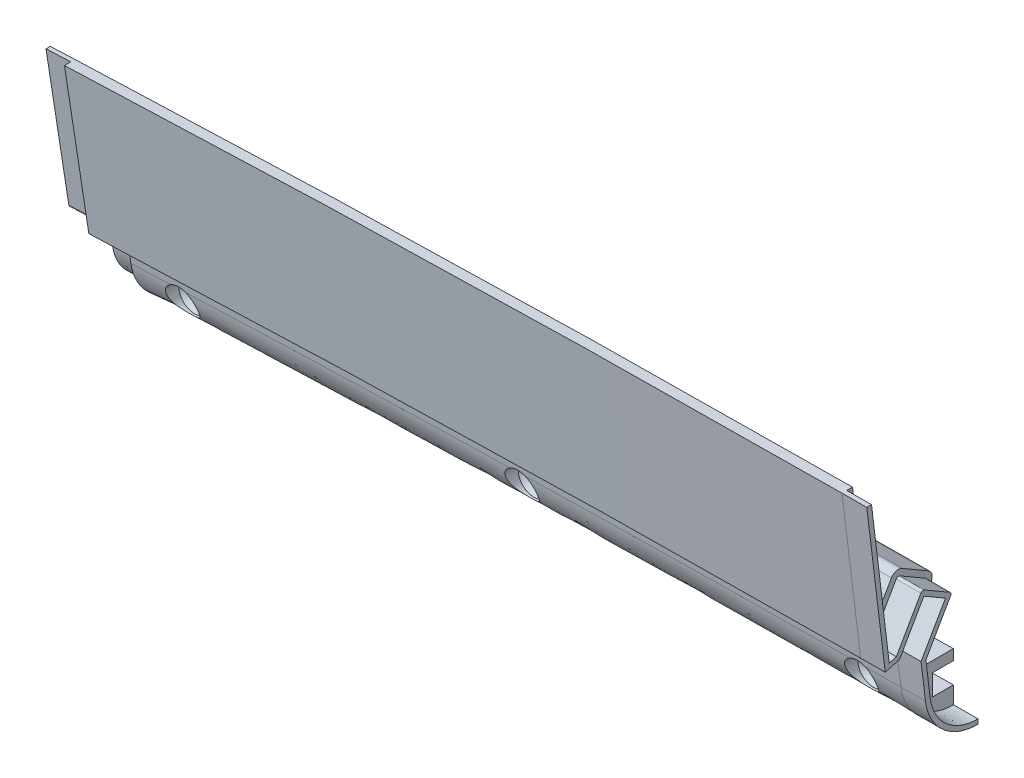
SolidWorks part; units mm, degrees
ref_plane "Front Plane" through (0, 0, 0) normal (0, 0, 1) x (1, 0, 0)
ref_plane "Top Plane" through (0, 0, 0) normal (0, 1, 0) x (1, 0, 0)
ref_plane "Right Plane" through (0, 0, 0) normal (1, 0, 0) x (0, 0, -1)
ref_plane "Plane3" through (-117.056, -3.871, 0) normal (0.9995, 0.0331, 0) x (0, 0, -1)
sketch "Sketch2" plane through (-117.056, -3.871, 0) normal (0.9995, 0.0331, 0) x (0, 0, -1)
  line L0 (-101.6, -41.1511) -> (-101.6, -45.9265)
  line L1 (-101.6, -41.1511) -> (-101.6, -45.9265)
  line L2 (-106.68, -45.9265) -> (-106.68, -50.6257)
  line L3 (-106.68, -45.9265) -> (-106.68, -50.6257)
  line L4 (-101.6, -50.6257) -> (-106.68, -50.6257)
  line L5 (-101.6, -50.6257) -> (-106.68, -50.6257)
  line L6 (-101.6, -50.6257) -> (-101.6, -56.1377)
  line L7 (-101.6, -50.6257) -> (-101.6, -56.1377)
  line L8 (-106.68, -45.9265) -> (-101.6, -45.9265)
  line L9 (-106.68, -45.9265) -> (-101.6, -45.9265)
  line L10 (-106.8705, -50.8162) -> (-108.9961, -53.9781) construction
  line L11 (-101.7905, -43.196) -> (-101.7905, -45.736)
  line L12 (-106.8705, -45.736) -> (-101.7905, -45.736)
  line L13 (-106.8705, -45.736) -> (-106.8705, -50.8162)
  line L14 (-101.7905, -50.8162) -> (-106.8705, -50.8162)
  line L15 (-101.7905, -50.8162) -> (-101.7905, -56.1377)
  line L16 (-101.7905, -43.196) -> (-101.6, -43.196)
  line L17 (-101.7905, -41.1511) -> (-101.7905, -45.736) construction
  line L18 (-120.8053, -33.0481) -> (-115.57, -36.0708)
  line L19 (-120.8053, -33.0481) -> (-115.57, -36.0708)
  line L20 (-109.601, -25.7318) -> (-114.8363, -22.709)
  line L21 (-109.601, -25.7318) -> (-114.8363, -22.709)
  line L22 (-114.8363, -22.709) -> (-120.8053, -33.0481)
  line L23 (-114.8363, -22.709) -> (-120.8053, -33.0481)
  line L24 (-115.57, -36.0708) -> (-109.601, -25.7318)
  line L25 (-115.57, -36.0708) -> (-109.601, -25.7318)
  line L26 (-115.57, -36.0708) -> (-114.523, -44.9291)
  line L28 (-118.1876, -34.5595) -> (-112.2186, -24.2204) construction
  line L29 (-114.6403, -39.5406) -> (-107.0838, -26.4518)
  line L30 (-107.7811, -23.8496) -> (-114.1162, -20.1918)
  line L31 (-116.7185, -20.8891) -> (-124.2749, -33.9778)
  line L33 (-106.1314, -24.8021) -> (-115.766, -19.2393) construction
  line L34 (-115.766, -19.2393) -> (-124.2749, -33.9778) construction
  line L35 (-114.6403, -39.5406) -> (-106.1314, -24.8021) construction
  line L36 (-124.2749, -33.9778) -> (-114.6403, -39.5406) construction
  line L37 (-112.9486, -36.6103) -> (-112.1701, -43.196)
  line L38 (-124.2749, -33.9778) -> (-128.0422, -2.1051)
  line L39 (-128.0422, -2.1051) -> (-132.6063, -0.4439)
  line L40 (-50.8, 0.7495) -> (-2184.4, 0.7495)
  line L41 (-125.822, 0.7495) -> (-133.442, 0.7495)
  line L42 (-122.1519, -30.3004) -> (-125.822, 0.7495)
  arc A0 (-114.523, -44.9291) -> (-101.7905, -56.1377) centre (-101.9108, -43.4383) ccw
  arc A2 (-114.1162, -20.1918) -> (-116.7185, -20.8891) centre (-115.0687, -21.8416) ccw
  arc A3 (-107.0838, -26.4518) -> (-107.7811, -23.8496) centre (-108.7336, -25.4993) ccw
  arc A4 (-133.442, 0.7495) -> (-132.6063, -0.4439) centre (-132.172, 0.7495) ccw
  point P21 (-107.6337, -51.6514)
  point P22 (0, 0)
  point P40 (994.1925, -42.034)
  point P41 (-133.442, 0.7495)
  point P42 (986.21, -13.8823)
  point P45 (980.8261, -8.8265)
  point P46 (985.0704, -9.8607)
  point P49 (-101.6, -43.196)
  dimension "D2" = 25.4
  dimension "D6" = 1.905
  dimension "D8" = 2.54
  dimension "D4" = 2.54
  dimension "D5" = 2.54
  dimension "D7" = 2.54
  dimension "D9" = 2.54
  dimension "D10" = 20
  dimension "D11" = 7.62
  dimension "D12" = 3.81
  dimension "D3" = 0.1905
sketch "Sketch3" plane through (0, 0, 101.6) normal (0, 0, 1) x (1, 0, 0)
  arc A0 (622.1039, -83.1998) -> (-622.1039, -83.1998) centre (0, -4954.4862) ccw construction
  arc A1 (622.1039, -83.1998) -> (-622.1039, -83.1998) centre (0, -4954.4862) ccw
sketch "Sketch4" plane through (-117.3306, 4.4304, 1117.6) normal (0.9995, 0.0331, 0) x (0, 0, -1)
  line L29 (1009.8189, -32.1556) -> (1003.4838, -28.4978) construction
  line L32 (1000.8815, -29.1951) -> (993.3251, -42.2838) construction
  line L35 (993.3251, -42.2838) -> (989.5578, -10.4111) construction
  line L50 (995.4481, -38.6064) -> (991.778, -7.5565) construction
  line L51 (1002.03, -44.3768) -> (1003.077, -53.235) construction
  line L52 (1015.8095, -59.1222) -> (1015.8095, -64.4437) construction
  line L53 (1015.8095, -59.1222) -> (1010.7295, -59.1222) construction
  line L54 (1010.7295, -54.042) -> (1010.7295, -59.1222) construction
  line L55 (1010.7295, -54.042) -> (1015.8095, -54.042) construction
  line L56 (1015.8095, -51.502) -> (1015.8095, -54.042) construction
  line L57 (1015.8095, -51.502) -> (1016, -51.502) construction
  line L58 (1004.6514, -44.9163) -> (1005.4299, -51.502) construction
  line L60 (1002.7637, -31.015) -> (996.7947, -41.3541) construction
  line L61 (1007.999, -34.0377) -> (1002.7637, -31.015) construction
  line L62 (1002.03, -44.3768) -> (1007.999, -34.0377) construction
  line L64 (991.5295, -5.4538) -> (988.9718, -5.4538)
  line L69 (1009.8189, -32.1556) -> (1003.4838, -28.4978)
  line L70 (1000.8815, -29.1951) -> (999.2724, -31.9822)
  line L71 (993.3251, -42.2838) -> (988.9718, -5.4538)
  line L74 (994.5502, -31.0104) -> (991.5295, -5.4538)
  line L75 (1002.03, -44.3768) -> (1003.077, -53.235)
  line L76 (1015.8095, -59.1222) -> (1015.8095, -64.4437)
  line L77 (1015.8095, -59.1222) -> (1010.7295, -59.1222)
  line L78 (1010.7295, -54.042) -> (1010.7295, -59.1222)
  line L79 (1010.7295, -54.042) -> (1015.8095, -54.042)
  line L80 (1015.8095, -51.502) -> (1015.8095, -54.042)
  line L81 (1015.8095, -51.502) -> (1007.6873, -51.502)
  line L82 (1004.7505, -45.7539) -> (1005.1649, -49.2601)
  line L84 (1002.7637, -31.015) -> (996.7947, -41.3541)
  line L85 (1007.999, -34.0377) -> (1002.7637, -31.015)
  line L86 (1002.03, -44.3768) -> (1007.999, -34.0377)
  line L87 (996.7947, -41.3541) -> (993.3251, -42.2838)
  line L88 (1005.0732, -44.1858) -> (1010.5162, -34.7578)
  arc A8 (1010.5162, -34.7578) -> (1009.8189, -32.1556) centre (1008.8664, -33.8053) ccw construction
  arc A9 (1003.4838, -28.4978) -> (1000.8815, -29.1951) centre (1002.5313, -30.1476) ccw construction
  arc A11 (1003.077, -53.235) -> (1015.8095, -64.4437) centre (1015.6892, -51.7443) ccw construction
  arc A12 (1010.5162, -34.7578) -> (1009.8189, -32.1556) centre (1008.8664, -33.8053) ccw
  arc A13 (1003.4838, -28.4978) -> (1000.8815, -29.1951) centre (1002.5313, -30.1476) ccw
  arc A15 (1003.077, -53.235) -> (1015.8095, -64.4437) centre (1015.6892, -51.7443) ccw
  arc A16 (1005.1649, -49.2601) -> (1007.6873, -51.502) centre (1007.6873, -48.962) ccw
  arc A17 (1004.7505, -45.7539) -> (1005.0732, -44.1858) centre (1007.2729, -45.4558) cw
  arc A18 (994.5502, -31.0104) -> (999.2724, -31.9822) centre (997.0727, -30.7122) ccw
  point P1 (0, 0)
  point P4 (984.1331, -6.5532)
  point P5 (984.1526, -6.6221)
  dimension "D2" = 2.54
  dimension "D1" = 36.83
sweep "Sweep3" add profiles "Sketch4" path "Sketch3"
sketch "Sketch5" plane through (0, 0, 101.7905) normal (0, 0, -1) x (-1, 0, 0)
  line L0 (211.6509, -4.1577) -> (0, -4954.4862) construction
  line L1 (0, -4954.4862) -> (22.6014, 0.3132) construction
  line L2 (117.0808, -1.0187) -> (0, -4954.4862) construction
  arc A1 (628.0925, -39.606) -> (-627.2635, -39.5001) centre (0, -4954.4862) ccw construction
  point P2 (117.0808, -12.1191)
  point P5 (0, 0)
  point P7 (0, 0)
  point P10 (0, 0)
  point P11 (0, 0)
  point P12 (25.8616, -1.8054)
  point P13 (20.8017, -1.7816)
  point P14 (0, 0)
  point P15 (117.0808, -3.4913)
  point P16 (117.0808, -1.0187)
  point P23 (0, 0)
  point P24 (0, 0)
  point P25 (0, 0)
  point P26 (0, 0)
  point P27 (0, 0)
ref_plane "Plane1" through (-211.4422, -9.0402, 0) normal (-0.9991, -0.0427, 0) x (0.0427, -0.9991, 0)
ref_plane "Plane2" through (-22.5995, -0.1031, 0) normal (1, 0.0046, 0) x (-0.0046, 1, 0)
other "SurfaceCut1"
other "SurfaceCut2"
sketch "Sketch8" plane through (-117.056, -3.871, 0) normal (0.9995, 0.0331, 0) x (0, 0, -1)
  line L0 (-106.8705, -50.8162) -> (-106.8705, -45.736)
  line L1 (-106.8705, -50.8162) -> (-106.8705, -45.736)
  line L2 (-106.8705, -48.2761) -> (-119.5705, -48.2761)
  line L3 (-119.5705, -48.2761) -> (-119.5705, -44.4661)
  line L4 (-119.5705, -44.4661) -> (-110.6805, -44.4661)
  line L5 (-110.6805, -44.4661) -> (-108.7755, -46.3711)
  line L6 (-108.7755, -46.3711) -> (-106.8705, -46.3711)
  line L7 (-119.5705, -48.2761) -> (-117.7248, -48.2761) construction
  dimension "D1" = 1.905
  dimension "D2" = 1.905
  dimension "D3" = 12.7
  dimension "D4" = 45
  dimension "D5" = 3.81
revolve "Cut-Revolve1" cut sketch "Sketch8" angle 360 about L7
sketch "Sketch9" plane through (0, 0, 106.8705) normal (0, 0, -1) x (-1, 0, 0)
  line L0 (198.0737, -52.2212) -> (197.8686, -57.297) construction
  line L1 (32.934, -48.3318) -> (32.8999, -53.4117) construction
  arc A1 (209.5755, -52.6994) -> (22.3798, -48.2723) centre (0, -4954.4862) ccw construction
  arc A2 (209.3585, -57.7748) -> (22.3566, -53.3522) centre (0, -4954.4862) ccw construction
  point P8 (197.9712, -54.7591)
  point P11 (0, -4954.4862)
  point P16 (115.4604, -52.1207)
  dimension "D1" = 82.55
  dimension "D2" = 82.55
sketch "Sketch10" plane through (0, 0, 106.8705) normal (0, 0, -1) x (-1, 0, 0)
  line L0 (32.934, -48.3318) -> (32.8999, -53.4117) construction
  point P0 (32.917, -50.8717)
  point P1 (197.9712, -54.7591)
pattern_sketch "Sketch-Pattern1" of "Cut-Revolve1" driven by "Sketch10"
sketch "Sketch12" plane through (0, 0, 101.7905) normal (0, 0, -1) x (-1, 0, 0)
  line L0 (22.3914, -45.7325) -> (0, -4954.4862) construction
  line L1 (0, -4954.4862) -> (16.4224, -45.7089) construction
  arc A1 (209.684, -50.1619) -> (22.3914, -45.7325) centre (0, -4954.4862) ccw construction
  arc A2 (22.3914, -45.7325) -> (16.4224, -45.7089) centre (0, -4954.4862) ccw
  dimension "D1" = 5.969
sketch "Sketch11" plane through (-22.5995, -0.1031, 0) normal (1, 0.0046, 0) x (0, 0, -1)
  line L0 (-127.4772, 0.4163) -> (-123.2949, -34.9662)
  line L1 (-123.2949, -34.9662) -> (-121.5584, -34.5009)
  line L2 (-121.5584, -34.5009) -> (-115.5722, -24.1324)
  line L3 (-114.7047, -23.8999) -> (-108.5896, -27.4305)
  line L4 (-108.3571, -28.298) -> (-114.3903, -38.7478)
  line L5 (-114.3903, -38.7478) -> (-113.3879, -47.2287)
  line L6 (-127.4931, 0.5505) -> (-123.2949, -34.9662) construction
  line L7 (-101.7905, -58.571) -> (-101.7905, -57.4281)
  line L8 (-101.7905, -53.2497) -> (-101.7905, -58.571) construction
  line L9 (-101.7905, -57.4281) -> (-101.8013, -57.4281)
  line L10 (-115.2547, -23.5824) -> (-108.0396, -27.748) construction
  line L11 (-108.0396, -27.748) -> (-114.3903, -38.7478) construction
  line L12 (-121.5584, -34.5009) -> (-115.2547, -23.5824) construction
  line L18 (-126.0705, 0.4163) -> (-128.6282, 0.4163)
  line L19 (-128.6282, 0.4163) -> (-124.2749, -36.4121)
  line L20 (-124.2749, -36.4121) -> (-120.8053, -35.4824)
  line L21 (-120.8053, -35.4824) -> (-114.8363, -25.1438)
  line L22 (-114.8363, -25.1438) -> (-109.601, -28.1664)
  line L23 (-109.601, -28.1664) -> (-115.57, -38.505)
  line L24 (-115.57, -38.505) -> (-114.523, -47.3628)
  line L25 (-101.7905, -58.571) -> (-101.7905, -53.2497)
  line L26 (-101.7905, -53.2497) -> (-106.8705, -53.2497)
  line L27 (-106.8705, -53.2497) -> (-106.8705, -48.1697)
  line L28 (-106.8705, -48.1697) -> (-101.7905, -48.1697)
  line L29 (-101.7905, -48.1697) -> (-101.7905, -45.6298)
  line L30 (-101.7905, -45.6298) -> (-109.9127, -45.6298)
  line L31 (-112.4351, -43.388) -> (-112.8495, -39.8821)
  line L32 (-112.5268, -38.314) -> (-107.0838, -28.8864)
  line L33 (-107.781, -26.2843) -> (-114.1162, -22.6267)
  line L34 (-116.7185, -23.324) -> (-118.3276, -26.111)
  line L35 (-123.0498, -25.1392) -> (-126.0705, 0.4163)
  line L36 (-127.4772, 0.4163) -> (-128.6282, 0.4163)
  line L37 (-128.6282, 0.4163) -> (-124.2749, -36.4121)
  line L38 (-124.2749, -36.4121) -> (-120.8053, -35.4824)
  line L39 (-120.8053, -35.4824) -> (-114.8363, -25.1438)
  line L40 (-114.8363, -25.1438) -> (-109.601, -28.1664)
  line L41 (-109.601, -28.1664) -> (-115.57, -38.505)
  line L42 (-115.57, -38.505) -> (-114.523, -47.3628)
  arc A0 (-108.5896, -27.4305) -> (-108.3571, -28.298) centre (-108.9071, -27.9805) cw
  arc A1 (-115.5722, -24.1324) -> (-114.7047, -23.8999) centre (-115.0222, -24.4499) cw
  arc A4 (-112.4351, -43.388) -> (-109.9127, -45.6298) centre (-109.9127, -43.0899) ccw
  arc A5 (-112.5268, -38.314) -> (-112.8495, -39.8821) centre (-110.3273, -39.5839) ccw
  arc A6 (-107.0838, -28.8864) -> (-107.781, -26.2843) centre (-108.7335, -27.934) ccw
  arc A7 (-114.1162, -22.6267) -> (-116.7185, -23.324) centre (-115.0687, -24.2765) ccw
  spline S0 degree 1 poles (-113.3879, -47.2287) (-101.8013, -57.4281) knots 0 0 1 1 construction
  spline S1 degree 3 poles (-113.3879, -47.2287) (-113.3048, -47.9315) (-113.0054, -49.3314) (-111.9316, -51.9222) (-109.7159, -54.7457) (-106.0351, -56.9465) (-103.2019, -57.4413) (-101.8013, -57.4281) knots 0 0 0 0 0.125 0.25 0.5 0.75 1 1 1 1
  spline S2 degree 3 poles (1806.7112, 500.659) (415.3182, 185.4234) (-128.7728, 19.3052) (-114.2511, -48.8982) (-114.1523, -49.2756) (-113.8076, -50.3834) (-113.513, -51.0946) (-112.7943, -52.4623) (-112.3662, -53.1223) (-111.4114, -54.3348) (-110.8822, -54.8941) (-110.0099, -55.6617) (-109.7043, -55.9068) (-109.0766, -56.3642) (-108.7542, -56.5771) (-107.762, -57.1697) (-107.0674, -57.5036) (-105.9744, -57.9102) (-105.6018, -58.0296) (-104.8546, -58.2318) (-104.4782, -58.3153) (-51.6561, -67.5546) (53.4105, 250.997) (369.459, 1883.482) knots -11.048432 -11.048432 -11.048432 -11.048432 0.0625 0.0625 0.125 0.125 0.25 0.25 0.375 0.375 0.5 0.5 0.5625 0.5625 0.625 0.625 0.75 0.75 0.8125 0.8125 0.875 0.875 9.519326 9.519326 9.519326 9.519326 only from (-114.523, -47.3628) to (-101.7905, -58.571)
  spline S3 degree 3 poles (-966.8365, -555.2864) (-146.5253, 43.3441) (-110.7563, -19.4511) (-119.0219, -26.9036) (-119.2485, -27.0513) (-119.7291, -27.2666) (-119.9898, -27.3374) (-120.3827, -27.3802) (-120.5144, -27.3844) (-120.779, -27.3719) (-120.9121, -27.3551) (-121.1705, -27.3017) (-121.297, -27.2651) (-121.5443, -27.1722) (-121.6661, -27.1152) (-121.896, -26.9847) (-122.0051, -26.911) (-122.2115, -26.7469) (-122.3097, -26.6555) (-122.5785, -26.3624) (-122.7254, -26.1414) (-131.5662, -6.8591) (104.7841, 84.3421) (817.0787, 315.6785) knots -5.03449 -5.03449 -5.03449 -5.03449 0.125 0.125 0.25 0.25 0.375 0.375 0.4375 0.4375 0.5 0.5 0.5625 0.5625 0.625 0.625 0.6875 0.6875 0.75 0.75 0.875 0.875 10.718854 10.718854 10.718854 10.718854 only from (-118.3276, -26.111) to (-123.0498, -25.1392)
  spline S4 degree 3 poles (-114.523, -47.3628) (-114.4771, -47.7506) (-114.4136, -48.1352) (-114.2511, -48.8982) (-114.1523, -49.2756) (-113.8076, -50.3834) (-113.513, -51.0946) (-112.7943, -52.4623) (-112.3662, -53.1223) (-111.4114, -54.3348) (-110.8822, -54.8941) (-110.0099, -55.6617) (-109.7043, -55.9068) (-109.0766, -56.3642) (-108.7542, -56.5771) (-107.762, -57.1697) (-107.0674, -57.5036) (-105.9744, -57.9102) (-105.6018, -58.0296) (-104.8546, -58.2318) (-104.4782, -58.3153) (-103.3407, -58.5143) (-102.5713, -58.5784) (-101.7905, -58.571) knots 0 0 0 0 0.0625 0.0625 0.125 0.125 0.25 0.25 0.375 0.375 0.5 0.5 0.5625 0.5625 0.625 0.625 0.75 0.75 0.8125 0.8125 0.875 0.875 1 1 1 1
  dimension "D3" = 0.635
  dimension "D1" = 0
  dimension "D2" = 1.143
sweep "Sweep4" add profiles "Sketch11" path "Sketch12"
sketch "Sketch14" plane through (-211.4422, -9.0402, 0) normal (-0.9991, -0.0427, 0) x (0, 0, 1)
  line L0 (113.0095, -42.7133) -> (113.9971, -34.3581)
  line L1 (113.9971, -34.3581) -> (107.5192, -23.138)
  line L2 (107.5192, -23.138) -> (115.3941, -18.5914)
  line L3 (115.3941, -18.5914) -> (121.8095, -29.7031)
  line L4 (121.8095, -29.7031) -> (122.9682, -30.0136)
  line L5 (122.9682, -30.0136) -> (127.1147, 5.0658)
  line L18 (128.6282, 4.8869) -> (126.0705, 4.8869)
  line L19 (126.0705, 4.8869) -> (123.0498, -20.6686)
  line L20 (118.3276, -21.6403) -> (116.7185, -18.8534)
  line L21 (114.1162, -18.1561) -> (107.7811, -21.8137)
  line L22 (107.0838, -24.4158) -> (112.5268, -33.8434)
  line L23 (112.8495, -35.4115) -> (112.4351, -38.9175)
  line L24 (109.9127, -41.1592) -> (101.7905, -41.1592)
  line L25 (101.7905, -41.1592) -> (101.7905, -43.6991)
  line L26 (101.7905, -43.6991) -> (106.8705, -43.6991)
  line L27 (106.8705, -43.6991) -> (106.8705, -48.7791)
  line L28 (106.8705, -48.7791) -> (101.7905, -48.7791)
  line L29 (101.7905, -48.7791) -> (101.7905, -54.1004)
  line L30 (114.523, -42.8922) -> (115.57, -34.0344)
  line L31 (115.57, -34.0344) -> (109.601, -23.6958)
  line L32 (109.601, -23.6958) -> (114.8363, -20.6732)
  line L33 (114.8363, -20.6732) -> (120.8053, -31.0118)
  line L34 (120.8053, -31.0118) -> (124.2749, -31.9414)
  line L35 (124.2749, -31.9414) -> (128.6282, 4.8869)
  line L36 (128.6282, 4.8869) -> (126.0705, 4.8869)
  line L37 (126.0705, 4.8869) -> (123.0498, -20.6686)
  line L38 (118.3276, -21.6403) -> (116.7185, -18.8534)
  line L39 (114.1162, -18.1561) -> (107.7811, -21.8137)
  line L40 (107.0838, -24.4158) -> (112.5268, -33.8434)
  line L41 (112.8495, -35.4115) -> (112.4351, -38.9175)
  line L42 (109.9127, -41.1592) -> (101.7905, -41.1592)
  line L43 (101.7905, -41.1592) -> (101.7905, -43.6991)
  line L44 (101.7905, -43.6991) -> (106.8705, -43.6991)
  line L45 (106.8705, -43.6991) -> (106.8705, -48.7791)
  line L46 (106.8705, -48.7791) -> (101.7905, -48.7791)
  line L47 (101.7905, -48.7791) -> (101.7905, -54.1004)
  line L48 (114.523, -42.8922) -> (115.57, -34.0344)
  line L49 (115.57, -34.0344) -> (109.601, -23.6958)
  line L50 (109.601, -23.6958) -> (114.8363, -20.6732)
  line L51 (114.8363, -20.6732) -> (120.8053, -31.0118)
  line L52 (120.8053, -31.0118) -> (124.2749, -31.9414)
  line L53 (124.2749, -31.9414) -> (128.6282, 4.8869)
  arc A4 (116.7185, -18.8534) -> (114.1162, -18.1561) centre (115.0687, -19.8059) ccw
  arc A5 (107.7811, -21.8137) -> (107.0838, -24.4158) centre (108.7335, -23.4634) ccw
  arc A6 (112.8495, -35.4115) -> (112.5268, -33.8434) centre (110.3273, -35.1133) ccw
  arc A7 (109.9127, -41.1592) -> (112.4351, -38.9175) centre (109.9127, -38.6193) ccw
  arc A8 (116.7185, -18.8534) -> (114.1162, -18.1561) centre (115.0687, -19.8059) ccw
  arc A9 (107.7811, -21.8137) -> (107.0838, -24.4158) centre (108.7335, -23.4634) ccw
  arc A10 (112.8495, -35.4115) -> (112.5268, -33.8434) centre (110.3273, -35.1133) ccw
  arc A11 (109.9127, -41.1592) -> (112.4351, -38.9175) centre (109.9127, -38.6193) ccw
  spline S0 degree 1 poles (101.8049, -52.5765) (113.0095, -42.7133) knots 0 0 1 1 construction
  spline S1 degree 3 poles (101.8049, -52.5765) (102.4893, -52.583) (103.8689, -52.4674) (106.4858, -51.7551) (109.4658, -49.9761) (112.0284, -46.7154) (112.8505, -44.0584) (113.0095, -42.7133) knots 0 0 0 0 0.125 0.25 0.5 0.75 1 1 1 1
  spline S2 degree 3 poles (-1420.2451, -2589.1907) (7.5348, 76.4537) (129.3579, -7.252) (122.7249, -21.671) (122.575, -21.8961) (122.2185, -22.2837) (122.0069, -22.4517) (121.6628, -22.6462) (121.5435, -22.702) (121.2955, -22.795) (121.1665, -22.8321) (120.908, -22.8851) (120.7774, -22.9014) (120.5134, -22.9137) (120.3791, -22.9094) (120.1163, -22.8803) (119.987, -22.8557) (119.7325, -22.7864) (119.6063, -22.7412) (119.2436, -22.578) (119.0214, -22.433) (93.7379, 0.421) (581.1886, 448.0858) (2362.312, 1968.4478) knots -7.286241 -7.286241 -7.286241 -7.286241 0.125 0.125 0.25 0.25 0.375 0.375 0.4375 0.4375 0.5 0.5 0.5625 0.5625 0.625 0.625 0.6875 0.6875 0.75 0.75 0.875 0.875 16.766809 16.766809 16.766809 16.766809 only from (123.0498, -20.6686) to (118.3276, -21.6403)
  spline S3 degree 3 poles (-288.3388, 2916.9987) (-102.777, 757.3692) (19.5454, -60.9671) (103.3479, -54.0254) (103.7348, -53.9753) (104.8774, -53.7738) (105.6202, -53.5717) (107.068, -53.0324) (107.777, -52.6914) (109.1008, -51.8981) (109.7227, -51.4442) (110.5948, -50.6762) (110.8766, -50.4042) (111.4099, -49.8396) (111.662, -49.5468) (112.3757, -48.6378) (112.795, -47.9912) (113.3369, -46.9586) (113.5026, -46.6041) (113.7979, -45.8886) (113.9285, -45.5258) (132.5439, 14.5864) (-288.4354, 203.7302) (-2703.1014, 979.8882) knots -13.349036 -13.349036 -13.349036 -13.349036 0.0625 0.0625 0.125 0.125 0.25 0.25 0.375 0.375 0.5 0.5 0.5625 0.5625 0.625 0.625 0.75 0.75 0.8125 0.8125 0.875 0.875 11.030088 11.030088 11.030088 11.030088 only from (101.7905, -54.1004) to (114.523, -42.8922)
  spline S4 degree 3 poles (123.0498, -20.6686) (123.0184, -20.9338) (122.9449, -21.1927) (122.7249, -21.671) (122.575, -21.8961) (122.2185, -22.2837) (122.0069, -22.4517) (121.6628, -22.6462) (121.5435, -22.702) (121.2955, -22.795) (121.1665, -22.8321) (120.908, -22.8851) (120.7774, -22.9014) (120.5134, -22.9137) (120.3791, -22.9094) (120.1163, -22.8803) (119.987, -22.8557) (119.7325, -22.7864) (119.6063, -22.7412) (119.2436, -22.578) (119.0214, -22.433) (118.6267, -22.0763) (118.4611, -21.8716) (118.3276, -21.6403) knots 0 0 0 0 0.125 0.125 0.25 0.25 0.375 0.375 0.4375 0.4375 0.5 0.5 0.5625 0.5625 0.625 0.625 0.6875 0.6875 0.75 0.75 0.875 0.875 1 1 1 1
  spline S5 degree 3 poles (101.7905, -54.1004) (102.1809, -54.1041) (102.5705, -54.0898) (103.3479, -54.0254) (103.7348, -53.9753) (104.8774, -53.7738) (105.6202, -53.5717) (107.068, -53.0324) (107.777, -52.6914) (109.1008, -51.8981) (109.7227, -51.4442) (110.5948, -50.6762) (110.8766, -50.4042) (111.4099, -49.8396) (111.662, -49.5468) (112.3757, -48.6378) (112.795, -47.9912) (113.3369, -46.9586) (113.5026, -46.6041) (113.7979, -45.8886) (113.9285, -45.5258) (114.2702, -44.4227) (114.4313, -43.6677) (114.523, -42.8922) knots 0 0 0 0 0.0625 0.0625 0.125 0.125 0.25 0.25 0.375 0.375 0.5 0.5 0.5625 0.5625 0.625 0.625 0.75 0.75 0.8125 0.8125 0.875 0.875 1 1 1 1
  dimension "D1" = 0
  dimension "D2" = 1.524
sketch "Sketch15" plane through (-211.4422, -9.0402, 0) normal (-0.9991, -0.0427, 0) x (0, 0, 1)
  line L0 (113.0095, -42.7133) -> (113.9971, -34.3581) construction
  line L1 (113.9971, -34.3581) -> (107.5192, -23.138) construction
  line L2 (107.5192, -23.138) -> (115.3941, -18.5914) construction
  line L3 (115.3941, -18.5914) -> (121.8095, -29.7031) construction
  line L4 (121.8095, -29.7031) -> (122.9682, -30.0136) construction
  line L5 (122.9682, -30.0136) -> (127.1147, 5.0658) construction
  line L6 (113.0095, -42.7133) -> (113.9724, -34.5675)
  line L7 (113.8917, -34.1755) -> (107.5192, -23.138)
  line L8 (107.5192, -23.138) -> (115.3941, -18.5914)
  line L9 (115.3941, -18.5914) -> (121.678, -29.4753)
  line L10 (122.0636, -29.7712) -> (122.2594, -29.8237)
  line L11 (123.0543, -29.2848) -> (127.0936, 4.8869)
  line L12 (101.7905, -48.7791) -> (101.7905, -54.1004) construction
  line L13 (101.7905, -48.7791) -> (101.7905, -52.5765)
  line L14 (101.8049, -52.5765) -> (101.7905, -52.5765)
  line L18 (124.2749, -31.9414) -> (128.6282, 4.8869)
  line L19 (128.6282, 4.8869) -> (126.0705, 4.8869)
  line L20 (126.0705, 4.8869) -> (123.0498, -20.6686)
  line L21 (118.3276, -21.6403) -> (116.7185, -18.8534)
  line L22 (114.1162, -18.1561) -> (107.7811, -21.8137)
  line L23 (107.0838, -24.4158) -> (112.5268, -33.8434)
  line L24 (112.8495, -35.4115) -> (112.4351, -38.9175)
  line L25 (109.9127, -41.1592) -> (101.7905, -41.1592)
  line L26 (101.7905, -41.1592) -> (101.7905, -43.6991)
  line L27 (101.7905, -43.6991) -> (106.8705, -43.6991)
  line L28 (106.8705, -43.6991) -> (106.8705, -48.7791)
  line L29 (106.8705, -48.7791) -> (101.7905, -48.7791)
  line L30 (101.7905, -48.7791) -> (101.7905, -54.1004)
  line L31 (114.523, -42.8922) -> (115.57, -34.0344)
  line L32 (115.57, -34.0344) -> (109.601, -23.6958)
  line L33 (109.601, -23.6958) -> (114.8363, -20.6732)
  line L34 (114.8363, -20.6732) -> (120.8053, -31.0118)
  line L35 (120.8053, -31.0118) -> (124.2749, -31.9414)
  line L37 (127.0936, 4.8869) -> (126.0705, 4.8869)
  line L38 (126.0705, 4.8869) -> (123.0498, -20.6686)
  line L39 (118.3276, -21.6403) -> (116.7185, -18.8534)
  line L40 (114.1162, -18.1561) -> (107.7811, -21.8137)
  line L41 (107.0838, -24.4158) -> (112.5268, -33.8434)
  line L42 (112.8495, -35.4115) -> (112.4351, -38.9175)
  line L43 (109.9127, -41.1592) -> (101.7905, -41.1592)
  line L44 (101.7905, -41.1592) -> (101.7905, -43.6991)
  line L45 (101.7905, -43.6991) -> (106.8705, -43.6991)
  line L46 (106.8705, -43.6991) -> (106.8705, -48.7791)
  line L47 (106.8705, -48.7791) -> (101.7905, -48.7791)
  arc A0 (113.9724, -34.5675) -> (113.8917, -34.1755) centre (113.3418, -34.493) ccw
  arc A1 (121.678, -29.4753) -> (122.0636, -29.7712) centre (122.2279, -29.1578) ccw
  arc A2 (122.2594, -29.8237) -> (123.0543, -29.2848) centre (122.4237, -29.2103) ccw
  arc A4 (116.7185, -18.8534) -> (114.1162, -18.1561) centre (115.0687, -19.8059) ccw
  arc A5 (107.7811, -21.8137) -> (107.0838, -24.4158) centre (108.7335, -23.4634) ccw
  arc A6 (112.8495, -35.4115) -> (112.5268, -33.8434) centre (110.3273, -35.1133) ccw
  arc A7 (109.9127, -41.1592) -> (112.4351, -38.9175) centre (109.9127, -38.6193) ccw
  arc A8 (116.7185, -18.8534) -> (114.1162, -18.1561) centre (115.0687, -19.8059) ccw
  arc A9 (107.7811, -21.8137) -> (107.0838, -24.4158) centre (108.7335, -23.4634) ccw
  arc A10 (112.8495, -35.4115) -> (112.5268, -33.8434) centre (110.3273, -35.1133) ccw
  arc A11 (109.9127, -41.1592) -> (112.4351, -38.9175) centre (109.9127, -38.6193) ccw
  spline S0 degree 3 poles (1969.6766, 654.3437) (8.5109, 56.766) (75.3403, -60.2329) (106.4858, -51.7551) (109.4658, -49.9761) (134.2797, -18.4018) (-16.091, 107.1074) (-926.156, -1745.3361) knots -5.450838 -5.450838 -5.450838 -5.450838 0.125 0.25 0.5 0.75 7.512309 7.512309 7.512309 7.512309 only from (101.8049, -52.5765) to (113.0095, -42.7133) construction
  spline S1 degree 3 poles (101.8049, -52.5765) (102.4893, -52.583) (103.8689, -52.4674) (106.4858, -51.7551) (109.4658, -49.9761) (112.0284, -46.7154) (112.8505, -44.0584) (113.0095, -42.7133) knots 0 0 0 0 0.125 0.25 0.5 0.75 1 1 1 1
  spline S2 degree 3 poles (-1420.2451, -2589.1907) (7.5348, 76.4537) (129.3579, -7.252) (122.7249, -21.671) (122.575, -21.8961) (122.2185, -22.2837) (122.0069, -22.4517) (121.6628, -22.6462) (121.5435, -22.702) (121.2955, -22.795) (121.1665, -22.8321) (120.908, -22.8851) (120.7774, -22.9014) (120.5134, -22.9137) (120.3791, -22.9094) (120.1163, -22.8803) (119.987, -22.8557) (119.7325, -22.7864) (119.6063, -22.7412) (119.2436, -22.578) (119.0214, -22.433) (93.7379, 0.421) (581.1886, 448.0858) (2362.312, 1968.4478) knots -7.286241 -7.286241 -7.286241 -7.286241 0.125 0.125 0.25 0.25 0.375 0.375 0.4375 0.4375 0.5 0.5 0.5625 0.5625 0.625 0.625 0.6875 0.6875 0.75 0.75 0.875 0.875 16.766809 16.766809 16.766809 16.766809 only from (123.0498, -20.6686) to (118.3276, -21.6403)
  spline S3 degree 3 poles (-93.3253, 926.6784) (-10.5613, 232.0775) (53.1389, -58.1844) (103.3479, -54.0254) (103.7348, -53.9753) (104.8774, -53.7738) (105.6202, -53.5717) (107.068, -53.0324) (107.777, -52.6914) (109.1008, -51.8981) (109.7227, -51.4442) (110.5948, -50.6762) (110.8766, -50.4042) (111.4099, -49.8396) (111.662, -49.5468) (112.3757, -48.6378) (112.795, -47.9912) (113.3369, -46.9586) (113.5026, -46.6041) (113.7979, -45.8886) (113.9285, -45.5258) (125.9187, -6.8076) (-43.2917, 84.8615) (-804.6708, 350.8867) knots -7.947776 -7.947776 -7.947776 -7.947776 0.0625 0.0625 0.125 0.125 0.25 0.25 0.375 0.375 0.5 0.5 0.5625 0.5625 0.625 0.625 0.75 0.75 0.8125 0.8125 0.875 0.875 7.39364 7.39364 7.39364 7.39364 only from (101.7905, -54.1004) to (114.523, -42.8922)
  spline S4 degree 3 poles (123.0498, -20.6686) (123.0184, -20.9338) (122.9449, -21.1927) (122.7249, -21.671) (122.575, -21.8961) (122.2185, -22.2837) (122.0069, -22.4517) (121.6628, -22.6462) (121.5435, -22.702) (121.2955, -22.795) (121.1665, -22.8321) (120.908, -22.8851) (120.7774, -22.9014) (120.5134, -22.9137) (120.3791, -22.9094) (120.1163, -22.8803) (119.987, -22.8557) (119.7325, -22.7864) (119.6063, -22.7412) (119.2436, -22.578) (119.0214, -22.433) (118.6267, -22.0763) (118.4611, -21.8716) (118.3276, -21.6403) knots 0 0 0 0 0.125 0.125 0.25 0.25 0.375 0.375 0.4375 0.4375 0.5 0.5 0.5625 0.5625 0.625 0.625 0.6875 0.6875 0.75 0.75 0.875 0.875 1 1 1 1
  dimension "D2" = 0.635
  dimension "D1" = 0
sketch "Sketch16" plane through (0, 0, 101.7905) normal (0, 0, -1) x (-1, 0, 0)
  arc A0 (215.6474, -50.4205) -> (209.684, -50.1619) centre (0, -4954.4862) ccw
  arc A1 (209.684, -50.1619) -> (22.3914, -45.7325) centre (0, -4954.4862) ccw construction
  point P7 (213.426, -50.1619)
  dimension "D1" = 5.969
sweep "Sweep5" add profiles "Sketch15" path "Sketch16"
